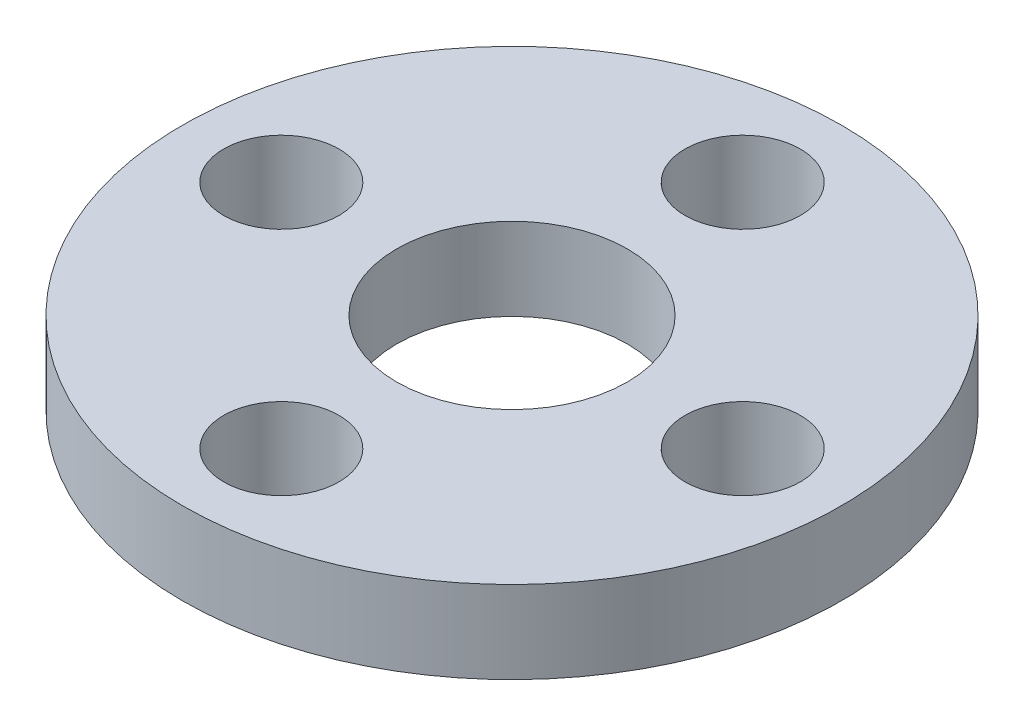
SolidWorks part; units mm, degrees
ref_plane "Спереди" through (0, 0, 0) normal (0, 0, 1) x (1, 0, 0)
ref_plane "Сверху" through (0, 0, 0) normal (0, 1, 0) x (1, 0, 0)
ref_plane "Справа" through (0, 0, 0) normal (1, 0, 0) x (0, 0, -1)
other "Configuration Table"
sketch "Эскиз1" plane through (0, 0, 0) normal (0, 1, 0) x (1, 0, 0)
  circle A0 centre (0, 0) radius 10
  circle A1 centre (0, 0) radius 7 construction
  circle A2 centre (-7, 0) radius 1.75
  circle A3 centre (0, 7) radius 1.75
  circle A4 centre (7, 0) radius 1.75
  circle A5 centre (0, -7) radius 1.75
  dimension "D1" = 20
  dimension "D2" = 14
  dimension "D3" = 3.5
extrude "Бобышка-Вытянуть1" add sketch "Эскиз1" along normal blind 2.5
sketch "Эскиз2" plane through (0, 2.5, 0) normal (0, 1, 0) x (1, 0, 0)
  circle A0 centre (0, 0) radius 3.5
  dimension "D1" = 7
extrude "Вырез-Вытянуть1" cut sketch "Эскиз2" against normal through all
